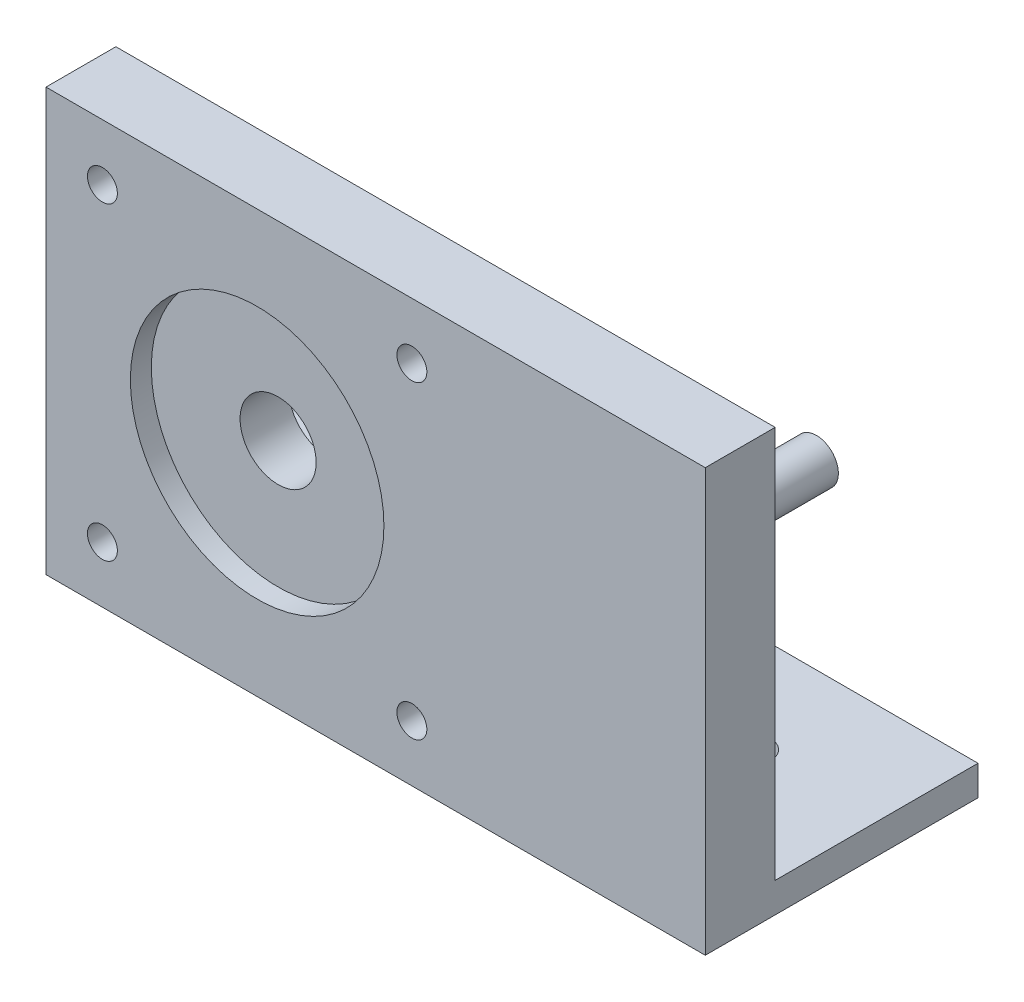
SolidWorks part; units mm, degrees
ref_plane "Front Plane" through (0, 0, 0) normal (0, 0, 1) x (1, 0, 0)
ref_plane "Top Plane" through (0, 0, 0) normal (0, 1, 0) x (1, 0, 0)
ref_plane "Right Plane" through (0, 0, 0) normal (1, 0, 0) x (0, 0, -1)
sketch "Sketch1" plane through (0, 0, 0) normal (1, 0, 0) x (0, 0, -1)
  line L0 (7, 3) -> (27.32, 3)
  line L1 (0, 0) -> (2.6604, 0)
  line L2 (0, 0) -> (0, 42.3)
  line L3 (0, 42.3) -> (7, 42.3)
  line L5 (27.32, 3) -> (27.32, 0)
  line L6 (27.32, 0) -> (2.6604, 0)
  line L7 (7, 42.3) -> (7, 3)
  dimension "D1" = 42.3
  dimension "D2" = 3
  dimension "D3" = 7
  dimension "D4" = 20.32
extrude "Boss-Extrude1" add sketch "Sketch1" along normal blind 66.04
sketch "Sketch2" plane through (0, 0, -7) normal (0, 0, -1) x (-1, 0, 0)
  line L0 (0, 3) -> (0, 42.3) construction
  line L1 (-36.65, 36.65) -> (-36.65, 5.65) construction
  line L2 (-5.65, 36.65) -> (-5.65, 5.65) construction
  line L3 (-66.04, 42.3) -> (0, 42.3) construction
  circle A0 centre (-5.65, 36.65) radius 1.5
  circle A1 centre (-5.65, 5.65) radius 1.5
  circle A2 centre (-36.65, 36.65) radius 1.5
  circle A3 centre (-36.65, 5.65) radius 1.5
  circle A4 centre (-21.15, 21.15) radius 3.81
  dimension "D2" = 7.62
  dimension "D4" = 15.5
  dimension "D5" = 21.15
  dimension "D10" = 3
  dimension "D11" = 3
  dimension "D12" = 3
  dimension "D13" = 3
  dimension "D1" = 21.15
  dimension "D3" = 31
  dimension "D6" = 15.5
  dimension "D7" = 15.5
  dimension "D8" = 15.5
  dimension "D9" = 15.5
sketch "Sketch3" plane through (0, 0, 0) normal (0, 0, 1) x (1, 0, 0)
  circle A0 centre (21.15, 21.15) radius 12.7
  dimension "D1" = 25.4
extrude "Cut-Extrude1" cut sketch "Sketch3" against normal blind 2.1
extrude "Cut-Extrude2" cut sketch "Sketch2" against normal through all
sketch "Sketch4" plane through (0, 0, -7) normal (0, 0, -1) x (-1, 0, 0)
  line L0 (-24.96, 21.15) -> (-16.7415, 21.15) construction
  circle A0 centre (-49.852, 21.15) radius 2.2
  circle A1 centre (-21.15, 21.15) radius 3.81 construction
  dimension "D2" = 4.4
  dimension "D1" = 28.702
extrude "Boss-Extrude2" add sketch "Sketch4" along normal blind 20.32
sketch "Sketch5" plane through (0, 0, -7) normal (0, 0, -1) x (-1, 0, 0)
  line L0 (-49.852, 21.15) -> (-21.15, 21.15) construction
  line L1 (-35.501, 21.15) -> (-35.501, 3) construction
  line L2 (-66.04, 3) -> (0, 3) construction
sketch "Sketch6" plane through (0, 3, 0) normal (0, 1, 0) x (1, 0, 0)
  line L0 (35.501, 7) -> (35.501, 25.2558) construction
  line L1 (49.852, 7) -> (21.15, 7) construction
  line L3 (29.3542, 7) -> (41.501, 7)
  line L4 (29.3542, 7) -> (29.3542, 19)
  line L5 (29.3542, 19) -> (41.501, 19)
  line L6 (41.501, 7) -> (41.501, 19)
  dimension "D1" = 6.1468
  dimension "D2" = 6
  dimension "D3" = 12
extrude "Cut-Extrude3" cut sketch "Sketch6" against normal through all
sketch "Sketch7" plane through (0, 0, -7) normal (0, 0, -1) x (-1, 0, 0)
  circle A0 centre (-36.65, 36.65) radius 2.8
  circle A1 centre (-36.65, 5.65) radius 2.8
  circle A2 centre (-5.65, 5.65) radius 2.8
  circle A3 centre (-5.65, 36.65) radius 2.8
  dimension "D1" = 5.6
  dimension "D2" = 5.6
  dimension "D3" = 5.6
  dimension "D4" = 5.6
extrude "Cut-Extrude4" cut sketch "Sketch7" against normal blind 1.27
sketch "Sketch8" plane through (0, 3, 0) normal (0, 1, 0) x (1, 0, 0)
  line L0 (20.3542, 27.32) -> (20.3542, 7) construction
  line L1 (66.04, 27.32) -> (0, 27.32) construction
  line L2 (29.3542, 7) -> (6.5542, 7) construction
  line L3 (53.501, 27.32) -> (53.501, 7) construction
  line L4 (66.04, 7) -> (0, 7) construction
  line L7 (29.3542, 19) -> (29.3542, 7) construction
  line L10 (41.501, 7) -> (41.501, 19) construction
  circle A0 centre (20.3542, 17.16) radius 1.925
  circle A1 centre (53.501, 17.16) radius 1.925
  dimension "D1" = 3.85
  dimension "D2" = 3.85
  dimension "D3" = 9
  dimension "D4" = 12
extrude "M4 bottom screws" cut sketch "Sketch8" against normal through all
sketch "Sketch10" plane through (0, 0, 0) normal (0, -1, 0) x (1, 0, 0)
  line L0 (41.501, -7) -> (41.501, -19) construction
  line L1 (41.501, -7) -> (41.501, -19)
  line L2 (41.501, -19) -> (29.3542, -19) construction
  line L3 (29.3542, -19) -> (29.3542, -7) construction
  line L4 (0, 0) -> (0, -27.32)
  line L5 (0, -27.32) -> (66.04, -27.32)
  line L6 (66.04, -27.32) -> (66.04, 0)
  line L7 (66.04, 0) -> (0, 0)
  line L8 (0, 0) -> (0, -27.32)
  line L9 (0, -27.32) -> (66.04, -27.32)
  line L10 (66.04, -27.32) -> (66.04, 0)
  line L11 (66.04, 0) -> (0, 0)
  line L12 (41.501, -19) -> (29.3542, -19)
  line L13 (29.3542, -19) -> (29.3542, -7)
  line L14 (29.3542, -7) -> (41.501, -7)
  circle A0 centre (53.501, -17.16) radius 1.925 construction
  circle A1 centre (20.3542, -17.16) radius 1.925 construction
  circle A2 centre (53.501, -17.16) radius 1.925
  circle A3 centre (20.3542, -17.16) radius 1.925
  dimension "D1" = 0
sketch "Sketch11" plane through (0, 0, 0) normal (0, -1, 0) x (-1, 0, 0)
  line L0 (-35.4276, 19) -> (-35.4276, 7) construction
  line L1 (-41.501, 19) -> (-29.3542, 19) construction
  line L2 (-29.3542, 7) -> (-41.501, 7) construction
  point P6 (-35.4276, 13)
